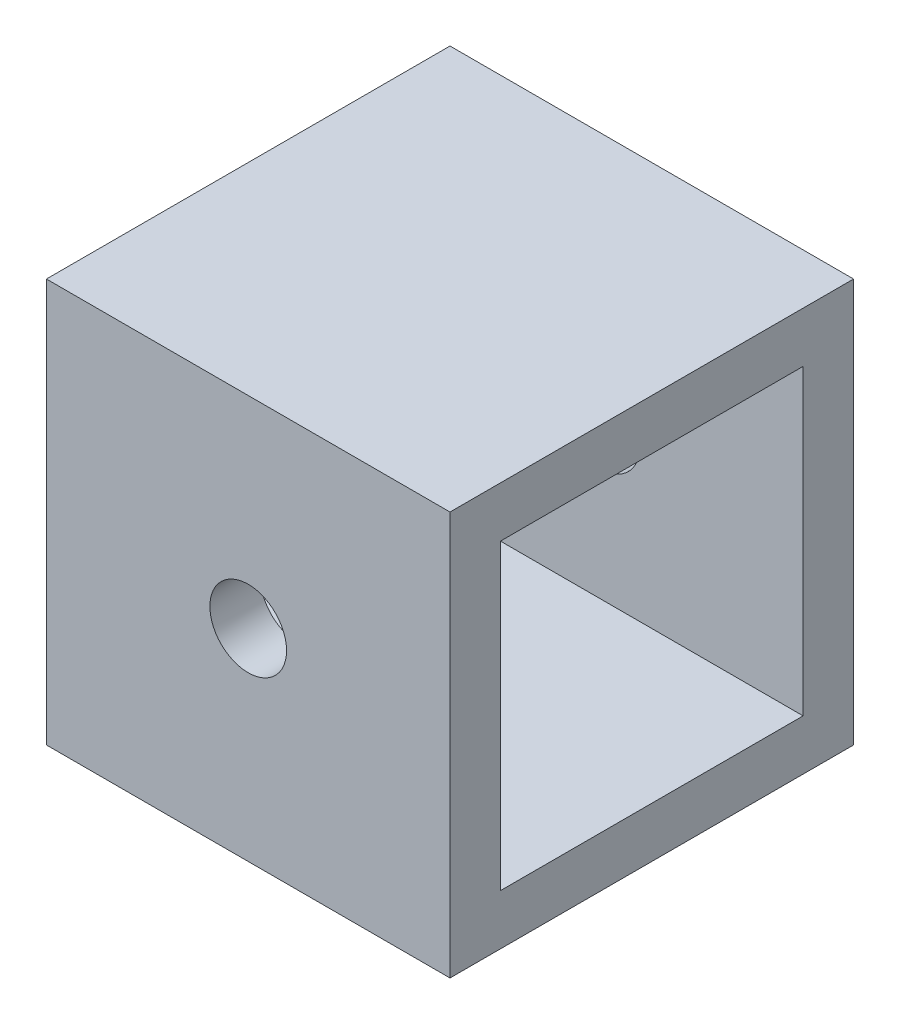
SolidWorks part; units mm, degrees
material "6061-T6 (SS)"
ref_plane "Front Plane" through (0, 0, 0) normal (0, 0, 1) x (1, 0, 0)
ref_plane "Top Plane" through (0, 0, 0) normal (0, 1, 0) x (1, 0, 0)
ref_plane "Right Plane" through (0, 0, 0) normal (1, 0, 0) x (0, 0, -1)
sketch "Sketch1" plane through (0, 0, 0) normal (1, 0, 0) x (0, 0, -1)
  line L1 (0, 0) -> (25.4, 0)
  line L2 (0, 0) -> (0, 25.4)
  line L3 (0, 25.4) -> (25.4, 25.4)
  line L4 (25.4, 0) -> (25.4, 25.4)
  dimension "D1" = 25.4
extrude "Extrude-Thin1" add sketch "Sketch1" along normal blind 25.4 thin thin type one direction reverse wall 3.175
sketch "Sketch2" plane through (0, 0, 0) normal (0, 0, 1) x (1, 0, 0)
  line L0 (0, 25.4) -> (0, 0) construction
  line L1 (25.4, 0) -> (0, 0) construction
  circle A0 centre (12.7, 12.7) radius 2.413
  dimension "D1" = 4.826
  dimension "D2" = 12.7
  dimension "D3" = 12.7
extrude "Cut-Extrude1" cut sketch "Sketch2" against normal through all
equation "\"Thick\"= \"in\""
